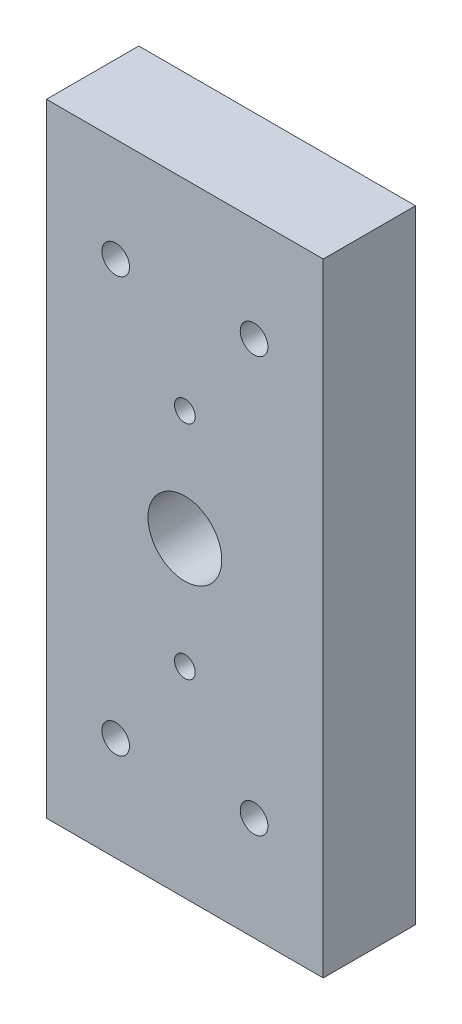
SolidWorks part; units mm, degrees
material "7079 Alloy"
ref_plane "Front" through (0, 0, 0) normal (0, 0, 1) x (1, 0, 0)
ref_plane "Top" through (0, 0, 0) normal (0, 1, 0) x (1, 0, 0)
ref_plane "Right" through (0, 0, 0) normal (1, 0, 0) x (0, 0, -1)
sketch "Sketch1" plane through (0, 0, 0) normal (0, 0, 1) x (1, 0, 0)
  line L0 (0, 135) -> (5, 135)
  line L1 (0, 0) -> (40, 0)
  line L2 (40, 135) -> (50, 135)
  line L3 (0, 135) -> (40, 135)
  line L4 (50, 135) -> (50, 0)
  line L5 (-429.9999, 91.4999) -> (470.0001, 91.4999) construction
  line L6 (-429.9999, 43.4999) -> (470.0001, 43.4999) construction
  line L7 (50, 0) -> (40, 0)
  line L8 (0, 135) -> (-10, 135)
  line L9 (-10, 135) -> (-10, 0)
  line L10 (-10, 0) -> (0, 0)
  circle A0 centre (5, 112.5) radius 3
  circle A3 centre (35, 112.5) radius 3
  circle A4 centre (5, 22.5) radius 3
  circle A7 centre (35, 22.5) radius 3
  circle A8 centre (20.0001, 91.4999) radius 2.25
  circle A9 centre (20.0001, 43.4999) radius 2.25
  dimension "D1" = 135
  dimension "D2" = 40
extrude "Extrude1" add sketch "Sketch1" along normal blind 20
sketch "Sketch2" plane through (0, 0, 0) normal (0, 0, -1) x (-1, 0, 0)
  circle A0 centre (-35, 112.5) radius 5
  circle A3 centre (-5, 112.5) radius 5
  circle A4 centre (-35, 22.5) radius 5
  circle A7 centre (-5, 22.5) radius 5
extrude "Cut-Extrude1" cut sketch "Sketch2" against normal blind 6
sketch "Sketch3" plane through (0, 0, 0) normal (0, 0, -1) x (-1, 0, 0)
  circle A0 centre (-20, 67.5) radius 8
extrude "Cut-Extrude2" cut sketch "Sketch3" against normal blind 20
sketch "Sketch4" plane through (0, 0, 0) normal (0, 0, -1) x (-1, 0, 0)
  line L1 (-40, 135) -> (-50, 135)
  line L2 (-40, 135) -> (-40, 0)
  line L3 (-40, 0) -> (-50, 0)
  line L4 (-50, 135) -> (-50, 0)
  line L5 (0, 135) -> (10, 135)
  line L6 (0, 135) -> (0, 0)
  line L7 (0, 0) -> (10, 0)
  line L8 (10, 135) -> (10, 0)
  dimension "D1" = 10
  dimension "D2" = 10
extrude "Extrude2" add sketch "Sketch4" against normal blind 20
